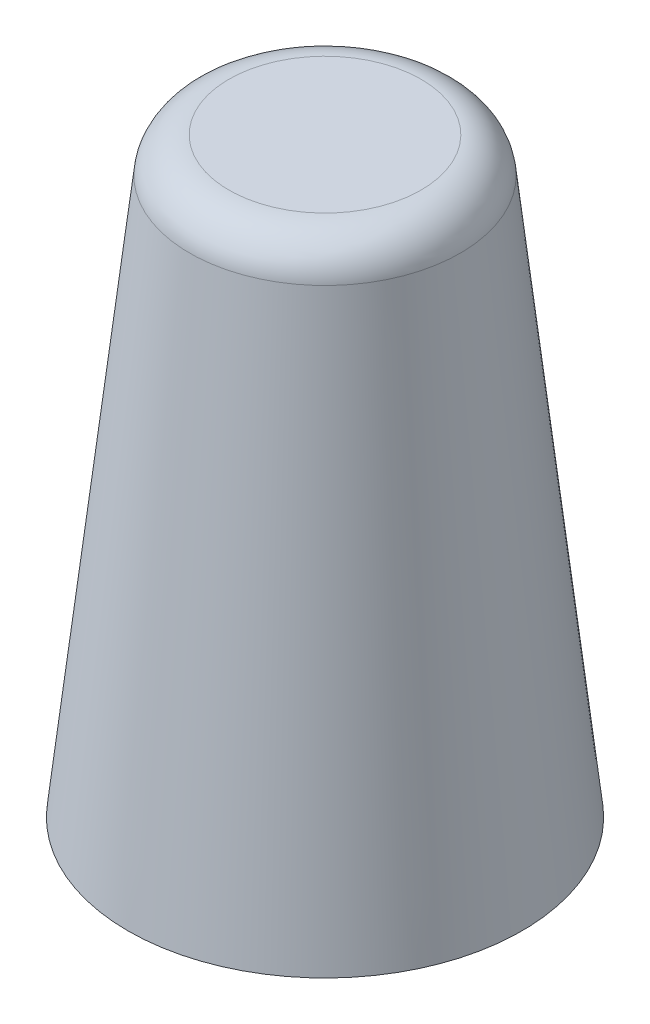
SolidWorks part; units mm, degrees
ref_plane "Спереди" through (0, 0, 0) normal (0, 0, 1) x (1, 0, 0)
ref_plane "Сверху" through (0, 0, 0) normal (0, 1, 0) x (1, 0, 0)
ref_plane "Справа" through (0, 0, 0) normal (1, 0, 0) x (0, 0, -1)
sketch "Эскиз1" plane through (0, 0, 0) normal (0, 0, 1) x (1, 0, 0)
  line L0 (0, 0) -> (0, 45)
  line L1 (0, 45) -> (7.3149, 45)
  line L2 (10.2965, 42.3313) -> (15, 0)
  line L3 (15, 0) -> (0, 0)
  arc A0 (10.2965, 42.3313) -> (7.3149, 45) centre (7.3149, 42) ccw
  point P7 (10, 45)
  dimension "D4" = 3
  dimension "D1" = 15
  dimension "D2" = 45
  dimension "D3" = 10
revolve "Повернуть1" add sketch "Эскиз1" angle 360 about L0
